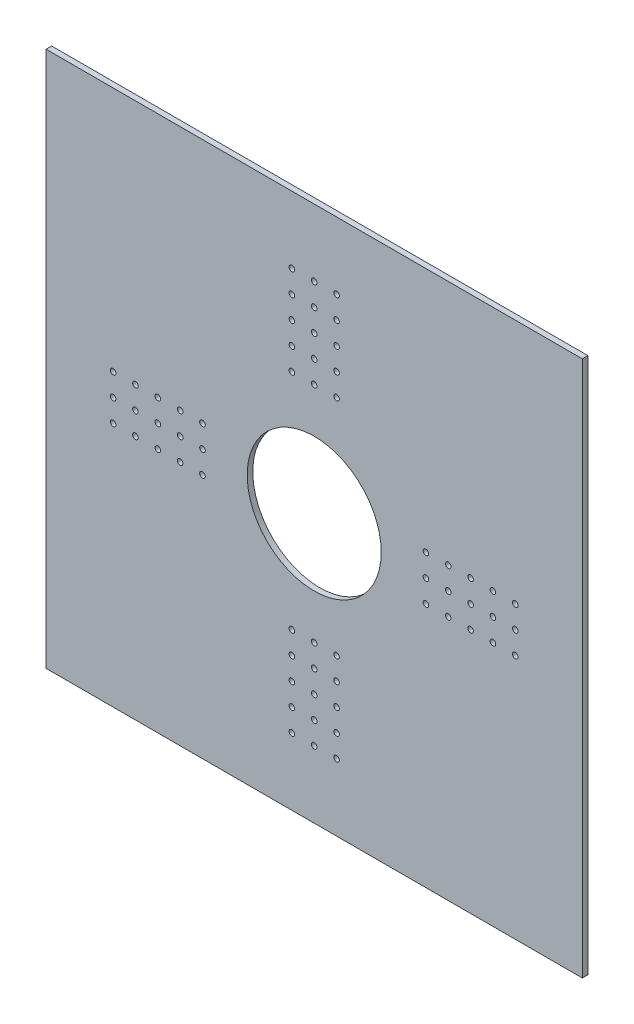
SolidWorks part; units mm, degrees
ref_plane "Front Plane" through (0, 0, 0) normal (0, 0, 1) x (1, 0, 0)
ref_plane "Top Plane" through (0, 0, 0) normal (0, 1, 0) x (1, 0, 0)
ref_plane "Right Plane" through (0, 0, 0) normal (1, 0, 0) x (0, 0, -1)
sketch "Sketch1" plane through (0, 0, 0) normal (0, 0, 1) x (1, 0, 0)
  line L5 (-304.8, -304.8) -> (304.8, -304.8)
  line L6 (-304.8, -304.8) -> (-304.8, 304.8)
  line L7 (-304.8, 304.8) -> (304.8, 304.8)
  line L8 (304.8, -304.8) -> (304.8, 304.8)
  line L9 (-304.8, -304.8) -> (304.8, 304.8) construction
  line L10 (-304.8, 304.8) -> (304.8, -304.8) construction
  circle A0 centre (0, 0) radius 76.2
  point P0 (49.2912, -162.1898)
  point P15 (0, 0)
  dimension "D2" = 152.4
  dimension "D1" = 609.6
extrude "Boss-Extrude1" add sketch "Sketch1" against normal blind 6.35
sketch "Sketch3" plane through (0, 0, 0) normal (0, 0, 1) x (1, 0, 0)
  line L0 (0, 0) -> (-127, 0) construction
  line L1 (-127, 25.4) -> (-127, -25.4) construction
  circle A0 centre (-127, 0) radius 3.175
  circle A1 centre (-127, 25.4) radius 3.175
  circle A2 centre (-127, -25.4) radius 3.175
  point P8 (-127, 0)
  dimension "D2" = 6.35
  dimension "D1" = 127
  dimension "D3" = 50.8
extrude "Cut-Extrude1" cut sketch "Sketch3" against normal up to next (6.35 mm away)
pattern_linear "LPattern1" count 5 spacing 25.4 along (-1, 0, 0) of "Cut-Extrude1"
pattern_circular "CirPattern1" count 4 over 360 about axis through (0, 0, 0) along (0, 0, 1) of "LPattern1", "Cut-Extrude1"
